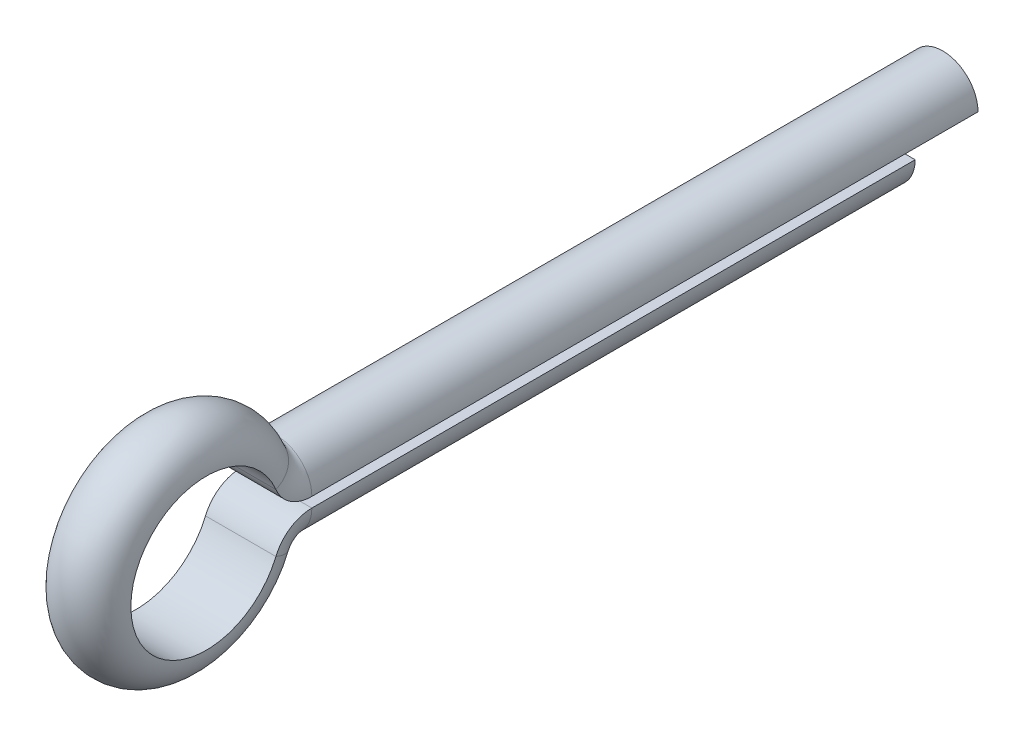
SolidWorks part; units mm, degrees
material "1.0545 (S355N)"
ref_plane "Płaszczyzna przednia" through (0, 0, 0) normal (0, 0, 1) x (1, 0, 0)
ref_plane "Płaszczyzna górna" through (0, 0, 0) normal (0, 1, 0) x (1, 0, 0)
ref_plane "Płaszczyzna prawa" through (0, 0, 0) normal (1, 0, 0) x (0, 0, -1)
sketch "Szkic1" plane through (0, 0, 0) normal (1, 0, 0) x (0, 0, -1)
  line L0 (0, 0) -> (-12, 0)
  arc A2 (-15.5, 0) -> (-12.8077, -0.5385) centre (-14.1, 0) ccw
  arc A4 (-12.8077, -0.5385) -> (-12, 0) centre (-12, -0.875) cw
  point P4 (0, 0)
  point P8 (-15.771, 0)
  dimension "D1" = 1.4
  dimension "D3" = 15.5
  dimension "D2" = 12
sketch "Szkic2" plane through (0, 0, 0) normal (0, 0, 1) x (1, 0, 0)
  line L0 (0, -1.4) -> (0, 0) construction
  line L1 (-0.7, -0.1) -> (0.7, -0.1)
  arc A0 (-0.7, -0.1) -> (0.7, -0.1) centre (0, -0.1) ccw
  point P1 (0, -0.0816)
  point P6 (0, 0)
  dimension "D1" = 0.7
  dimension "D2" = 0.1
sweep "Wyciągnięcie po ścieżce1" add profiles "Szkic2" path "Szkic1"
mirror "Lustro1" about plane through (0, 0, 0) normal (0, 1, 0) of "Wyciągnięcie po ścieżce1"
sketch "Szkic3" plane through (0, 0, 0) normal (0, 0, -1) x (-1, 0, 0)
  line L0 (0.7, 0.1) -> (-0.7, 0.1) construction
  line L1 (0.7, 0.1) -> (-0.7, 0.1)
  arc A0 (0.7, 0.1) -> (-0.7, 0.1) centre (0, 0.1) ccw construction
  arc A1 (0.7, 0.1) -> (-0.7, 0.1) centre (0, 0.1) ccw
extrude "Dodanie-wyciągnięcie1" add sketch "Szkic3" along normal blind 1.25
